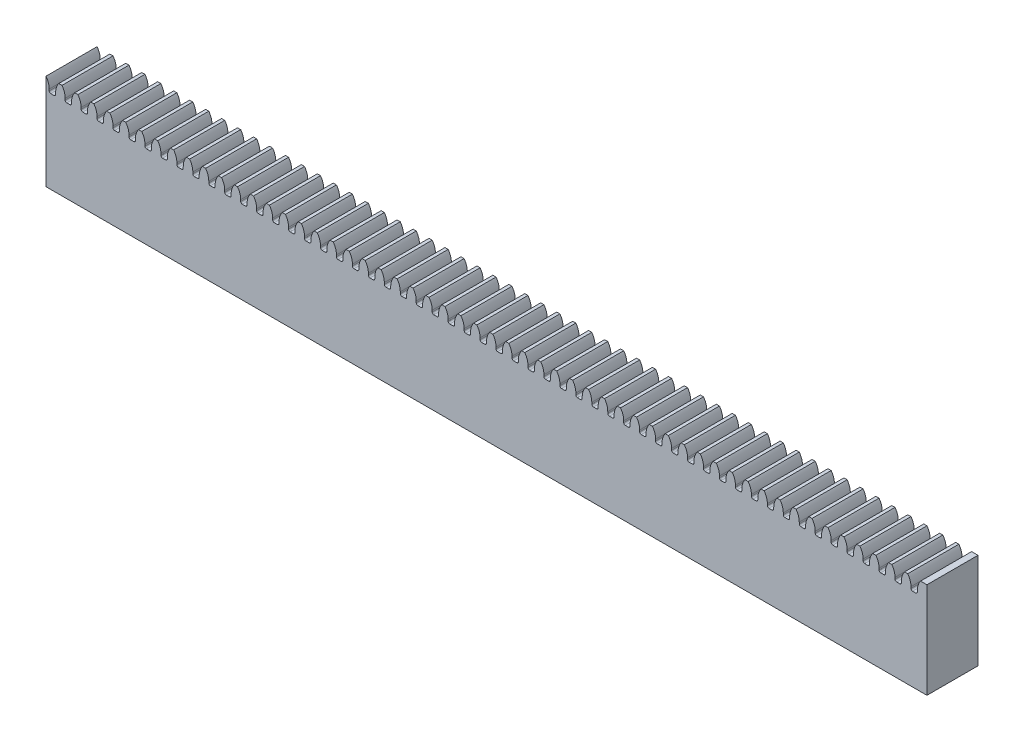
SolidWorks part; units mm, degrees
ref_plane "Face" through (0, 0, 0) normal (0, 0, 1) x (1, 0, 0)
ref_plane "Dessus" through (0, 0, 0) normal (0, 1, 0) x (1, 0, 0)
ref_plane "Droite" through (0, 0, 0) normal (1, 0, 0) x (0, 0, -1)
sketch "Esquisse1" plane through (0, 0, 0) normal (0, 1, 0) x (1, 0, 0)
  line L1 (0, 0) -> (138, 0)
  line L2 (0, 0) -> (0, 8)
  line L3 (0, 8) -> (138, 8)
  line L4 (138, 0) -> (138, 8)
  dimension "D1" = 138
  dimension "D2" = 8
extrude "Extrusion1" add sketch "Esquisse1" along normal blind 15
sketch "Esquisse2" plane through (0, 0, 0) normal (0, 0, 1) x (1, 0, 0)
  line L0 (0, 15) -> (2, 15)
  line L3 (1, 15) -> (1, 13) construction
  line L4 (0, 15) -> (138, 15) construction
  line L5 (0.5, 13.5) -> (0.5, 13)
  line L6 (0.5, 13) -> (1.5, 13)
  line L7 (1, 14) -> (0, 14) construction
  line L8 (0, 15) -> (0, 0) construction
  line L9 (0, 0) -> (138, 0) construction
  line L10 (1.5, 13.5) -> (1.5, 13)
  arc A0 (0.5, 13.5) -> (0, 15) centre (-2, 13.5) ccw
  arc A1 (1.5, 13.5) -> (2, 15) centre (4, 13.5) cw
  dimension "D1" = 14
  dimension "D2" = 0.5
  dimension "D3" = 0.5
  dimension "D4" = 0.5
extrude "Extrusion2" cut sketch "Esquisse2" against normal up to next (8 mm away)
fillet "Congé2" radius 0.25 2 edges at (0.5, 13, -4) (1.5, 13, -4)
pattern_linear "Répétition linéaire2" count 55 spacing 2.5 along (1, 0, 0) of "Extrusion2", "Congé2"
